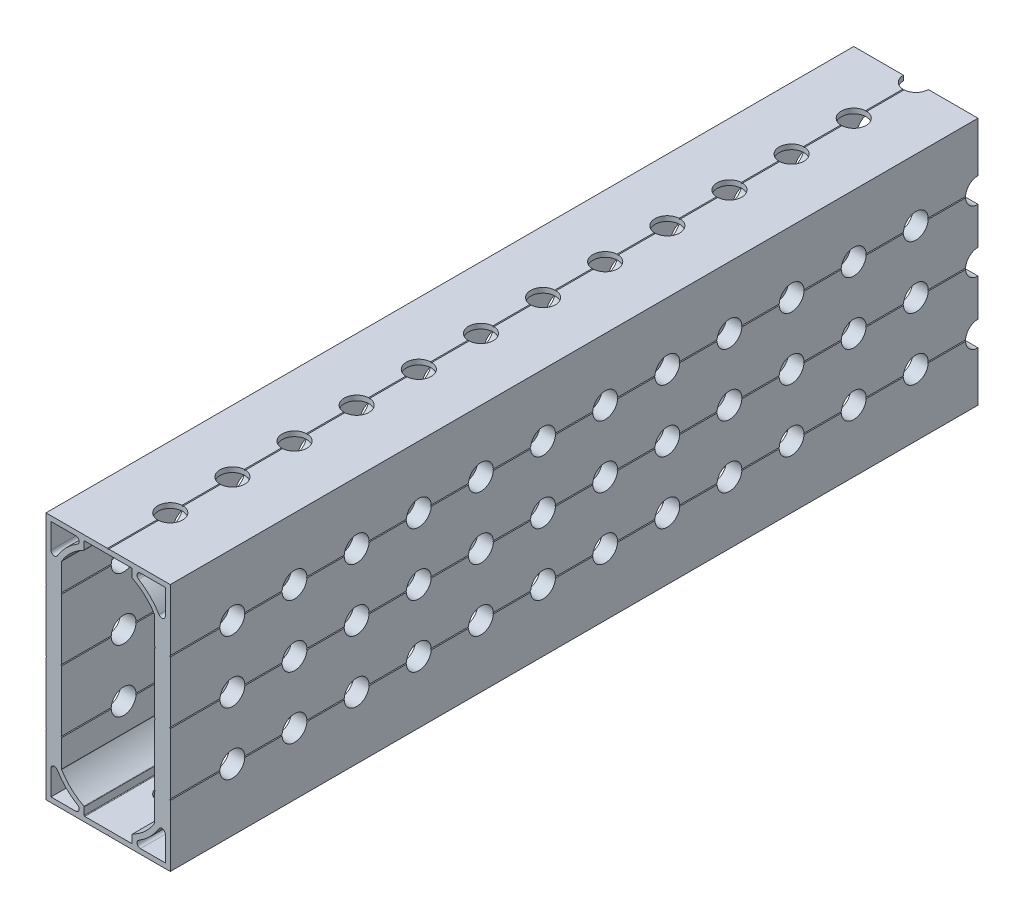
SolidWorks part; units mm, degrees
material "6061 Alloy"
ref_plane "Front Plane" through (0, 0, 0) normal (0, 0, 1) x (1, 0, 0)
ref_plane "Top Plane" through (0, 0, 0) normal (0, 1, 0) x (1, 0, 0)
ref_plane "Right Plane" through (0, 0, 0) normal (1, 0, 0) x (0, 0, -1)
other "Configuration Table"
ref_plane "Plane1" through (-12.7, 0, 0) normal (-1, 0, 0) x (0, -1, 0)
sketch "Sketch1" plane through (-12.7, 0, 0) normal (-1, 0, 0) x (0, -1, 0)
  line L0 (-25.4, -82.55) -> (25.4, -82.55)
  line L1 (25.4, -82.55) -> (25.4, 82.55)
  line L2 (25.4, 82.55) -> (-25.4, 82.55)
  line L3 (-25.4, 82.55) -> (-25.4, -82.55)
  line L4 (-25.4, -82.55) -> (25.4, 82.55) construction
  point P6 (0, 0)
  dimension "D1" = 50.8
  dimension "D2" = 165.1
extrude "Boss-Extrude1" add sketch "Sketch1" against normal blind 25.4
sketch "Sketch2" plane through (0, 0, -82.55) normal (0, 0, -1) x (-1, 0, 0)
  line L0 (-12.7, -12.573) -> (-12.7, -12.827)
  line L1 (-12.7, -12.827) -> (-12.573, -12.7)
  line L2 (-12.573, -12.7) -> (-12.7, -12.573)
  line L5 (-0.127, 0) -> (0.127, 0)
  line L6 (0.127, 0) -> (0, 0.127)
  line L7 (0, 0.127) -> (-0.127, 0)
  line L8 (-12.7, -25.4) -> (12.7, -25.4) construction
  line L9 (-12.7, 25.4) -> (-12.7, -25.4) construction
  line L10 (12.7, -12.827) -> (12.7, -12.573)
  line L11 (12.7, -12.573) -> (12.573, -12.7)
  line L12 (12.573, -12.7) -> (12.7, -12.827)
  line L13 (12.7, 25.4) -> (12.7, -25.4) construction
  line L17 (-12.7, 0.127) -> (-12.7, -0.127)
  line L18 (-12.7, -0.127) -> (-12.573, 0)
  line L19 (-12.573, 0) -> (-12.7, 0.127)
  line L20 (-12.7, 12.827) -> (-12.7, 12.573)
  line L21 (-12.7, 12.573) -> (-12.573, 12.7)
  line L22 (-12.573, 12.7) -> (-12.7, 12.827)
  line L23 (12.7, -0.127) -> (12.7, 0.127)
  line L24 (12.7, 0.127) -> (12.573, 0)
  line L25 (12.573, 0) -> (12.7, -0.127)
  line L26 (12.7, 12.573) -> (12.7, 12.827)
  line L27 (12.7, 12.827) -> (12.573, 12.7)
  line L28 (12.573, 12.7) -> (12.7, 12.573)
  line L29 (-0.127, 25.4) -> (0.127, 25.4)
  line L30 (0.127, 25.4) -> (0, 25.273)
  line L31 (0, 25.273) -> (-0.127, 25.4)
  line L32 (-12.7, 25.4) -> (12.7, 25.4) construction
  point P3 (-12.7, -12.7)
  point P10 (0, 0)
  point P31 (-12.7, 0)
  point P36 (-12.7, 12.7)
  dimension "D1" = 0.254
  dimension "D2" = 12.7
  dimension "D3" = 25.4
  dimension "D4" = 38.1
  dimension "D6" = 0.127
  dimension "D7" = 0.254
extrude "Cut-Extrude1" cut sketch "Sketch2" against normal through all
sketch "Sketch10" plane through (0, 0, 82.55) normal (0, 0, 1) x (1, 0, 0)
  line L0 (-11.684, 24.384) -> (-11.684, 19.2971)
  line L1 (-6.5971, 24.384) -> (-11.684, 24.384)
  line L2 (-0.127, 25.4) -> (-12.7, 25.4) construction
  line L3 (-12.7, 0.127) -> (-12.7, 0)
  line L5 (-12.7, 12.827) -> (-12.573, 12.7)
  line L6 (-12.7, 12.827) -> (-12.7, 12.573)
  line L10 (0.127, 25.4) -> (0, 25.273)
  line L11 (0, 25.273) -> (-0.127, 25.4)
  line L12 (-0.127, 25.4) -> (0.127, 25.4)
  line L13 (-12.573, 12.7) -> (-12.7, 12.573)
  line L18 (-12.7, -25.4) -> (-12.7, -12.827) construction
  line L19 (12.7, -25.4) -> (-12.7, -25.4) construction
  line L43 (-12.7, 0) -> (-12.573, 0)
  line L55 (0, 24.384) -> (-4.8895, 24.384)
  line L56 (-4.8895, 24.384) -> (-4.8895, 22.679)
  line L57 (-9.525, 18.4238) -> (-9.525, 12.827)
  line L58 (-9.525, 12.827) -> (-9.652, 12.7)
  line L59 (-9.652, 12.7) -> (-9.525, 12.573)
  line L60 (-9.525, 12.573) -> (-9.525, 0.127)
  line L61 (-9.525, 0.127) -> (-9.652, 0)
  line L70 (12.7, 25.4) -> (0.127, 25.4) construction
  line L71 (-12.573, 0) -> (-12.7, 0.127)
  line L72 (-12.7, 0.127) -> (-12.7, 12.573) construction
  line L73 (-9.652, 0) -> (0, 0)
  line L74 (0, 0) -> (0, 24.384)
  arc A0 (-11.684, 19.2971) -> (-10.3994, 18.9412) centre (-10.9924, 19.2971) ccw
  arc A1 (-10.3994, 18.9412) -> (-6.2412, 23.0994) centre (0, 12.7) cw
  arc A2 (-6.2412, 23.0994) -> (-6.5971, 24.384) centre (-6.5971, 23.6924) ccw
  arc A8 (-4.8895, 22.679) -> (-9.525, 18.4238) centre (0, 12.7) ccw
  dimension "D1" = 0.6916
  dimension "D2" = 12.1285
  dimension "D3" = 45
  dimension "D11" = 11.1125
  dimension "D12" = 1.016
  dimension "D4" = 1.016
  dimension "D5" = 2.3006
  dimension "D6" = 0.127
  dimension "D7" = 25.4
  dimension "D8" = 1.016
  dimension "D9" = 45
  dimension "D10" = 3.175
  dimension "D13" = 4.8895
extrude "Cut-Extrude9" cut sketch "Sketch10" against normal through all
mirror "Mirror1" about plane through (0, 0, 0) normal (0, 1, 0) of "Cut-Extrude9" second plane through (0, 0, 0) second plane normal (1, 0, 0)
sketch "Sketch17" plane through (12.7, 0, 0) normal (1, 0, 0) x (0, 0, -1)
  line L0 (-82.55, 12.7) -> (82.55, 12.7) construction
  line L3 (-82.55, 0.127) -> (-82.55, 12.573) construction
  circle A0 centre (-69.85, 12.7) radius 2.54
  dimension "D2" = 5.08
  dimension "D1" = 12.7
sketch "Sketch18" plane through (0, 25.4, 0) normal (0, 1, 0) x (1, 0, 0)
  line L0 (0, -82.55) -> (0, 82.55) construction
  line L1 (12.7, -82.55) -> (0.127, -82.55) construction
  circle A0 centre (0, -69.85) radius 2.54
  dimension "D1" = 5.08
  dimension "D2" = 12.7
extrude "Cut-Extrude11" cut sketch "Sketch17" against normal through all and the other way through all
extrude "Cut-Extrude12" cut sketch "Sketch18" against normal through all
pattern_linear "LPattern1" count 14 spacing 12.7 along (0, 0, -1) of "Cut-Extrude12"
pattern_linear "LPattern2" count 14 spacing 12.7 along (0, 0, -1) count 3 spacing 12.7 along (0, -1, 0) of "Cut-Extrude11"
fillet "Fillet1" radius 0.127 12 edges at (-4.8895, 22.679, 0) (-4.8895, 24.384, 0) (-9.525, 18.4238, 0) (4.8895, 24.384, 0) (4.8895, 22.679, 0) (9.525, 18.4238, 0) (-4.8895, -24.384, 0) (-4.8895, -22.679, 0) (-9.525, -18.4238, 0) (4.8895, -22.679, 0) (4.8895, -24.384, 0) (9.525, -18.4238, 0)
equation "\"Length\"=6.5"
equation "\"D2@Sketch1\"=\"Length\""
